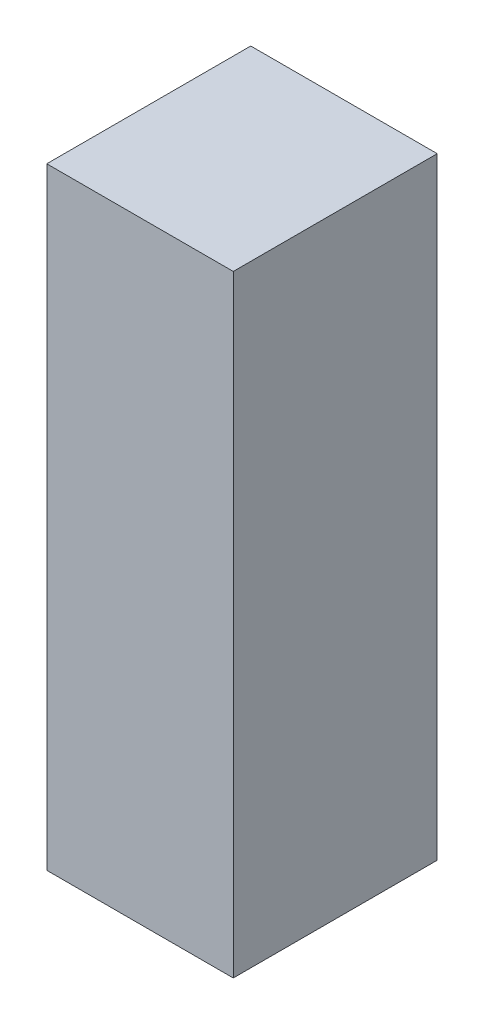
SolidWorks part; units mm, degrees
ref_plane "Front Plane" through (0, 0, 0) normal (0, 0, 1) x (1, 0, 0)
ref_plane "Top Plane" through (0, 0, 0) normal (0, 1, 0) x (1, 0, 0)
ref_plane "Right Plane" through (0, 0, 0) normal (1, 0, 0) x (0, 0, -1)
sketch "Sketch1" plane through (0, 0, 0) normal (0, 1, 0) x (1, 0, 0)
  line L1 (0, 0) -> (32, 0)
  line L2 (0, 0) -> (0, 35)
  line L3 (0, 35) -> (32, 35)
  line L4 (32, 0) -> (32, 35)
  dimension "D1" = 32
  dimension "D2" = 35
extrude "Boss-Extrude1" add sketch "Sketch1" along normal blind 105
